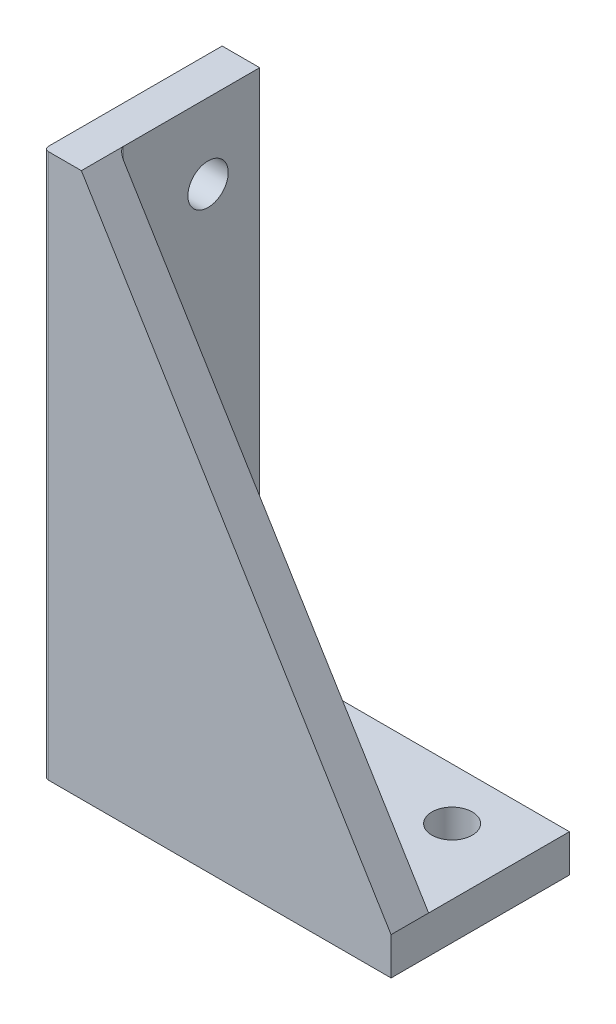
SolidWorks part; units mm, degrees
material "80% - PLA"
ref_plane "Front Plane" through (0, 0, 0) normal (0, 0, 1) x (1, 0, 0)
ref_plane "Top Plane" through (0, 0, 0) normal (0, 1, 0) x (1, 0, 0)
ref_plane "Right Plane" through (0, 0, 0) normal (1, 0, 0) x (0, 0, -1)
sketch "Sketch1" plane through (0, 0, 0) normal (0, 0, 1) x (1, 0, 0)
  line L1 (0, 0) -> (37, 0)
  line L2 (0, 0) -> (0, 58)
  line L3 (0, 58) -> (37, 58)
  line L4 (37, 0) -> (37, 58)
  dimension "D1" = 58
  dimension "D2" = 37
extrude "Boss-Extrude1" add sketch "Sketch1" along normal blind 30
sketch "Sketch2" plane through (0, 58, 0) normal (0, 1, 0) x (1, 0, 0)
  line L0 (37, -15) -> (0, -15)
  line L1 (37, -30) -> (37, 0) construction
  line L2 (0, -30) -> (0, 0) construction
  line L3 (37, -13) -> (0, -13)
  line L4 (37, -17) -> (0, -17)
  line L5 (37, 0) -> (0, 0) construction
  line L6 (37, 0) -> (4, 0)
  line L7 (37, 0) -> (37, -13)
  line L8 (37, -13) -> (4, -13)
  line L9 (4, 0) -> (4, -13)
  line L11 (37, -30) -> (4, -30)
  line L12 (37, -30) -> (37, -17)
  line L13 (37, -17) -> (4, -17)
  line L14 (4, -30) -> (4, -17)
  line M3 (37, 0) -> (0, 0)
  line M4 (0, 0) -> (0, -30)
  line M5 (0, -30) -> (37, -30)
  line M6 (37, -30) -> (37, 0)
  dimension "D3" = 33
  dimension "D4" = 33
  dimension "D1" = 2
  dimension "D2" = 2
extrude "Cut-Extrude1" cut sketch "Sketch2" against normal blind 54 contours L9 L3 M3 M6 | L14 L4 M5 M6 | L14 L4 M5 M4
sketch "Sketch3" plane through (0, 0, 13) normal (0, 0, 1) x (1, 0, 0)
  line L0 (4, 58) -> (37, 4)
  line L1 (37, 4) -> (37, 58)
  line L2 (37, 58) -> (4, 58)
  dimension "D1" = 33
extrude "Cut-Extrude2" cut sketch "Sketch3" along normal blind 46
hole_wizard "M4 Clearance Hole1" positions "Sketch5" profile "Sketch4" hole size "M4" standard "ISO" end condition through all
sketch "Sketch5" plane through (4, 0, 0) normal (1, 0, 0) x (0, 0, -1)
  line L0 (0, 58) -> (-13, 58) construction
  line L1 (-13, 4) -> (0, 4) construction
  line L6 (0, 4) -> (0, 58) construction
  point P3 (-3.5, 14)
  point P5 (-3.5, 50)
  dimension "D1" = 8
  dimension "D2" = 10
  dimension "D7" = 3.5
  dimension "D8" = 3.5
sketch "Sketch4" plane through (4, 14, 3.5) normal (0, 1, 0) x (0, 0, -1)
  line L0 (0, 0) -> (0, 4)
  line L1 (0, 4) -> (2.15, 4)
  line L2 (2.15, 4) -> (2.15, 0)
  line L5 (2.15, 0) -> (0, 0)
  line L11 (0, -6.35) -> (0, 107.95) construction
  dimension "Thru Hole Dia." = 4.3
  dimension "Thru Hole Depth" = 4
hole_wizard "M4 Clearance Hole2" positions "Sketch7" profile "Sketch6" hole size "M4" standard "ISO" end condition through all
sketch "Sketch7" plane through (0, 4, 0) normal (0, 1, 0) x (1, 0, 0)
  line L0 (37, 0) -> (4, 0) construction
  line L1 (4, 0) -> (4, -13) construction
  line L2 (37, -13) -> (37, 0) construction
  point P0 (12, -3.5)
  point P2 (30, -3.5)
  dimension "D1" = 3.5
  dimension "D2" = 8
  dimension "D3" = 7
  dimension "D4" = 3.5
sketch "Sketch6" plane through (12, 4, 3.5) normal (1, 0, 0) x (0, 0, 1)
  line L0 (0, 0) -> (0, 4)
  line L1 (0, 4) -> (2.15, 4)
  line L2 (2.15, 4) -> (2.15, 0)
  line L5 (2.15, 0) -> (0, 0)
  line L11 (0, -6.35) -> (0, 107.95) construction
  dimension "Thru Hole Dia." = 4.3
  dimension "Thru Hole Depth" = 4
sketch "Sketch8" plane through (0, 4, 0) normal (0, 1, 0) x (1, 0, 0)
  line L1 (0, -17) -> (37, -17)
  line L2 (0, -17) -> (0, -30)
  line L3 (0, -30) -> (37, -30)
  line L4 (37, -17) -> (37, -30)
extrude "Cut-Extrude3" cut sketch "Sketch8" against normal blind 10
fillet "Fillet1" radius 0.5 2 edges at (4, 31, 13) (0, 29, 17)
sketch "Sketch9" plane through (0, 0, 0) normal (0, 0, -1) x (-1, 0, 0)
  line L0 (-4, 58) -> (0, 58)
  line L1 (0, 58) -> (0, 0)
  line L2 (0, 0) -> (-37, 0)
  line L3 (-37, 0) -> (-37, 4)
  line L4 (-37, 4) -> (-4, 4)
  line L5 (-4, 4) -> (-4, 58)
extrude "Boss-Extrude2" add sketch "Sketch9" along normal blind 2
